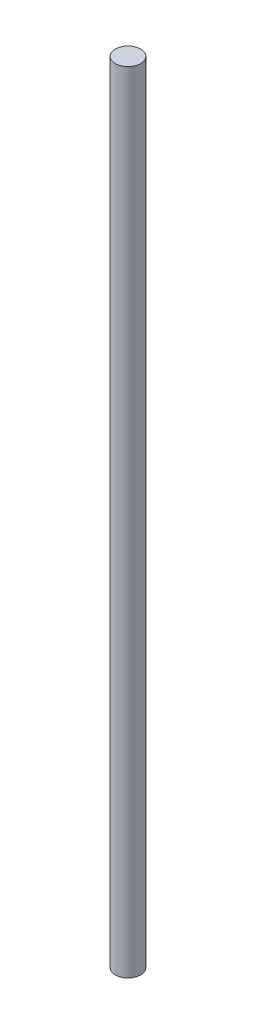
SolidWorks part; units mm, degrees
ref_plane "Front Plane" through (0, 0, 0) normal (0, 0, 1) x (1, 0, 0)
ref_plane "Top Plane" through (0, 0, 0) normal (0, 1, 0) x (1, 0, 0)
ref_plane "Right Plane" through (0, 0, 0) normal (1, 0, 0) x (0, 0, -1)
sketch "Sketch1" plane through (0, 0, 0) normal (0, 1, 0) x (1, 0, 0)
  circle A0 centre (-5.1341, 4.6555) radius 4
  dimension "D1" = 8
extrude "Boss-Extrude1" add sketch "Sketch1" along normal blind 250
